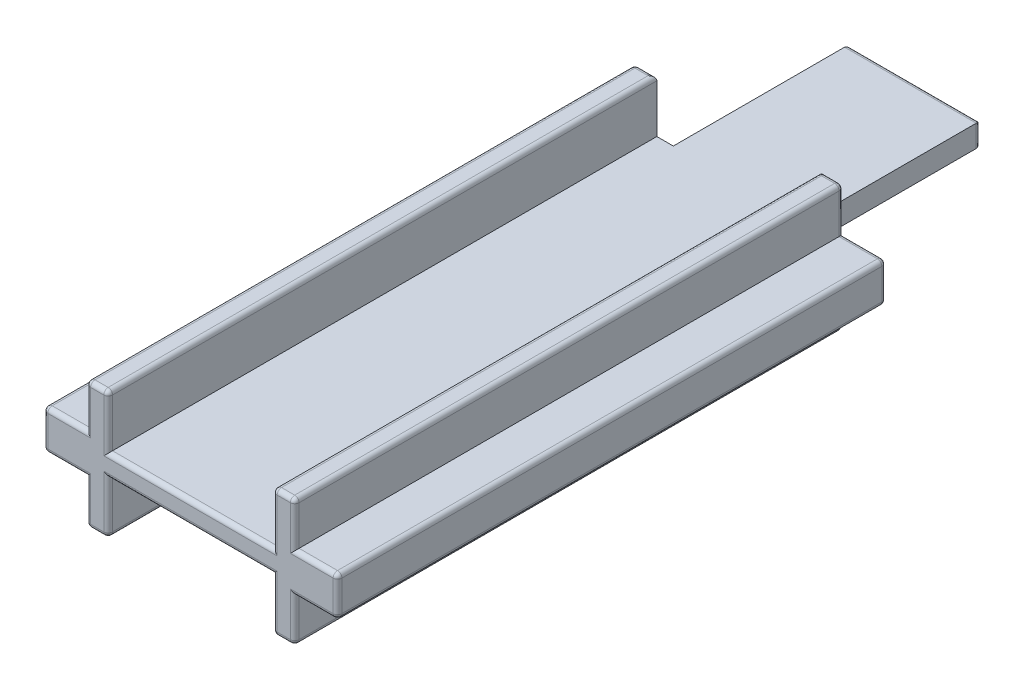
SolidWorks part; units mm, degrees
ref_plane "Ebene vorne" through (0, 0, 0) normal (0, 0, 1) x (1, 0, 0)
ref_plane "Ebene oben" through (0, 0, 0) normal (0, 1, 0) x (1, 0, 0)
ref_plane "Ebene rechts" through (0, 0, 0) normal (1, 0, 0) x (0, 0, -1)
sketch "Skizze1" plane through (0, 0, 0) normal (0, 0, 1) x (1, 0, 0)
  line L0 (-4.75, 0.9) -> (-6.7, 0.9)
  line L1 (6.7, -0.9) -> (4.75, -0.9)
  line L2 (6.7, -0.9) -> (6.7, 0.9)
  line L3 (6.7, 0.9) -> (4.75, 0.9)
  line L4 (-6.7, -0.9) -> (-6.7, 0.9)
  line L5 (6.7, -0.9) -> (-6.7, 0.9) construction
  line L6 (6.7, 0.9) -> (-6.7, -0.9) construction
  line L7 (-4.75, -2.9) -> (-3.75, -2.9)
  line L8 (-4.75, -2.9) -> (-4.75, -0.9)
  line L9 (-4.75, 2.9) -> (-3.75, 2.9)
  line L10 (-3.75, -2.9) -> (-3.75, -0.9)
  line L11 (-4.75, -2.9) -> (-3.75, 2.9) construction
  line L12 (-4.75, 2.9) -> (-3.75, -2.9) construction
  line L13 (4.75, -2.9) -> (3.75, -2.9)
  line L14 (4.75, -2.9) -> (4.75, -0.9)
  line L15 (4.75, 2.9) -> (3.75, 2.9)
  line L16 (3.75, -2.9) -> (3.75, -0.9)
  line L17 (4.75, -2.9) -> (3.75, 2.9) construction
  line L18 (4.75, 2.9) -> (3.75, -2.9) construction
  line L19 (-4.75, -0.9) -> (-6.7, -0.9)
  line L20 (-4.75, 0.9) -> (-4.75, 2.9)
  line L21 (-3.75, 0.9) -> (-3.75, 2.9)
  line L22 (3.75, -0.9) -> (-3.75, -0.9)
  line L23 (3.75, 0.9) -> (3.75, 2.9)
  line L24 (4.75, 0.9) -> (4.75, 2.9)
  line L25 (3.75, 0.9) -> (-3.75, 0.9)
  point P0 (0, 0)
  point P5 (-4.25, 0)
  point P11 (4.25, 0)
  dimension "D1" = 1.8
  dimension "D2" = 5.8
  dimension "D3" = 13.4
  dimension "D4" = 9.5
  dimension "D5" = 1
  dimension "D6" = 4.75
extrude "Aufsatz-Linear austragen1" add sketch "Skizze1" along normal blind 25
sketch "Skizze2" plane through (0, 0, 0) normal (0, 0, -1) x (-1, 0, 0)
  line L0 (-3.75, 0.9) -> (3.75, 0.9) construction
  line L1 (3, -0.9) -> (-3, -0.9)
  line L2 (3, -0.9) -> (3, 0.9)
  line L3 (3, 0.9) -> (-3, 0.9)
  line L4 (-3, -0.9) -> (-3, 0.9)
  line L5 (3, -0.9) -> (-3, 0.9) construction
  line L6 (3, 0.9) -> (-3, -0.9) construction
  point P0 (0, 0)
  dimension "D1" = 6
extrude "Aufsatz-Linear austragen2" add sketch "Skizze2" along normal blind 8
sketch "Skizze3" plane through (0, 0, 25) normal (0, 0, 1) x (1, 0, 0)
  line L1 (-3.75, -0.9) -> (3.75, -0.9)
  line L2 (-3.75, -0.9) -> (-3.75, -0.5)
  line L3 (-3.75, -0.5) -> (3.75, -0.5)
  line L4 (3.75, -0.9) -> (3.75, -0.5)
  line L5 (3.75, 0.9) -> (-3.75, 0.9)
  line L6 (3.75, 0.9) -> (3.75, 0.5)
  line L7 (3.75, 0.5) -> (-3.75, 0.5)
  line L8 (-3.75, 0.9) -> (-3.75, 0.5)
  dimension "D1" = 1
  dimension "D2" = 0.5
extrude "Schnitt-Linear austragen1" cut sketch "Skizze3" against normal through all
fillet "Verrundung1" radius 0.2 50 edges at (-5.725, 0.9, 25) (-4.75, 1.9, 25) (-3.75, 1.7, 25) (3.75, 1.7, 25) (4.75, 1.9, 25) (5.725, 0.9, 25) (5.725, -0.9, 25) (4.75, -1.9, 25) (3.75, -1.7, 25) (-3.75, -1.7, 25) (-4.75, -1.9, 25) (-5.725, -0.9, 25) (-3, 0, -8) (3, 0, -8) (-6.7, 0.9, 12.5) (-6.7, 0, 25) (-6.7, -0.9, 12.5) (-6.7, 0, 0) (6.7, -0.9, 12.5) (6.7, 0, 25) (6.7, 0.9, 12.5) (6.7, 0, 0) (-4.75, -2.9, 12.5) (-3.75, -2.9, 12.5) (-4.25, -2.9, 0) (3.75, -2.9, 12.5) (4.75, -2.9, 12.5) (4.25, -2.9, 0) (-3.75, 2.9, 12.5) (-4.75, 2.9, 12.5) (-4.25, 2.9, 0) (4.75, 2.9, 12.5) (3.75, 2.9, 12.5) (4.25, 2.9, 0) (4.75, 1.9, 0) (5.725, 0.9, 0) (5.725, -0.9, 0) (4.75, -1.9, 0) (-4.75, 1.9, 0) (-4.75, -1.9, 0) (-5.725, 0.9, 0) (-5.725, -0.9, 0) (-4.25, -2.9, 25) (4.25, -2.9, 25) (-4.25, 2.9, 25) (4.25, 2.9, 25) (0, 0.5, 25) (0, -0.5, 25) (0, 0.5, -8) (0, -0.5, -8)
